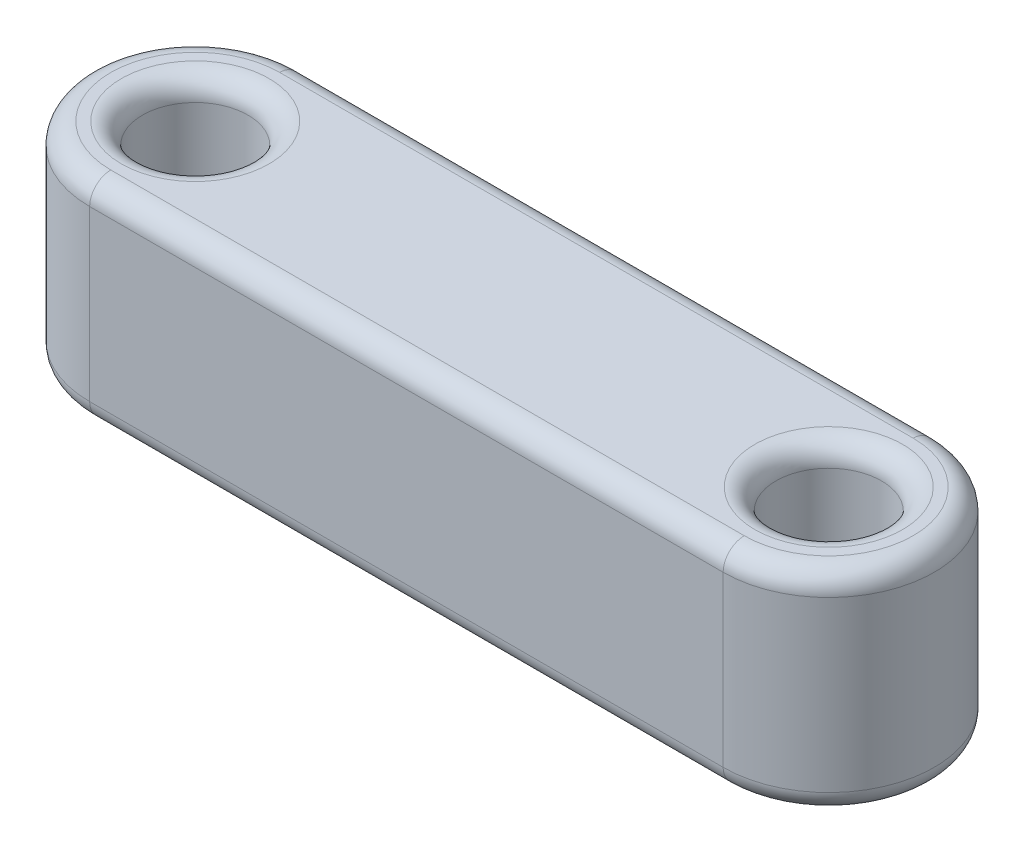
SolidWorks part; units mm, degrees
ref_plane "Front Plane" through (0, 0, 0) normal (0, 0, 1) x (1, 0, 0)
ref_plane "Top Plane" through (0, 0, 0) normal (0, 1, 0) x (1, 0, 0)
ref_plane "Right Plane" through (0, 0, 0) normal (1, 0, 0) x (0, 0, -1)
sketch "Sketch1" plane through (0, 0, 0) normal (0, 1, 0) x (1, 0, 0)
  line L0 (0, 0) -> (30, 0) construction
  line L1 (0, 5) -> (30, 5)
  line L2 (0, -5) -> (30, -5)
  arc A0 (0, 5) -> (0, -5) centre (0, 0) ccw
  arc A1 (30, -5) -> (30, 5) centre (30, 0) ccw
  circle A2 centre (0, 0) radius 2.5
  circle A3 centre (30, 0) radius 2.5
  point P3 (15, 0)
  dimension "D1" = 5
  dimension "D3" = 5
  dimension "D4" = 5
  dimension "D2" = 30
extrude "Boss-Extrude1" add sketch "Sketch1" along normal blind 10
fillet "Fillet1" radius 1 12 edges at (30, 0, 2.5) (0, 0, 2.5) (15, 0, 5) (35, 0, 0) (15, 0, -5) (-5, 0, 0) (30, 10, 2.5) (15, 10, -5) (35, 10, 0) (15, 10, 5) (-5, 10, 0) (0, 10, 2.5)
